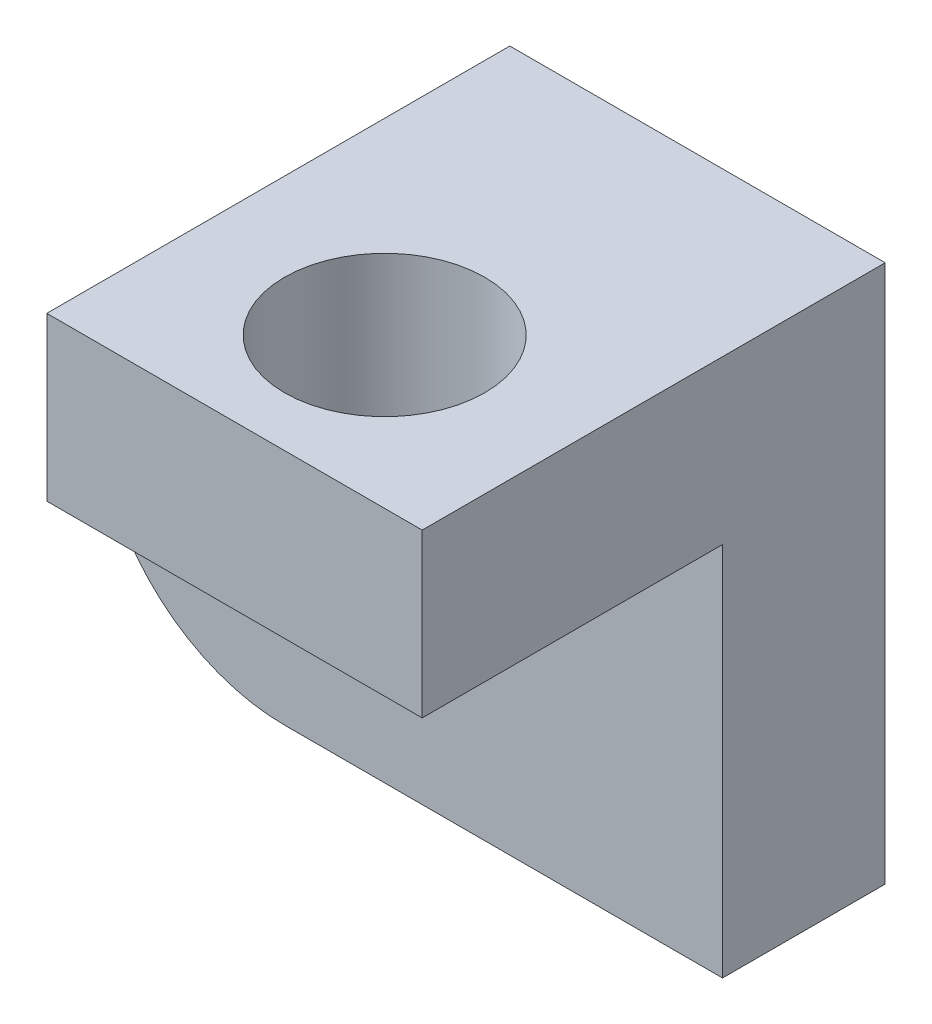
SolidWorks part; units mm, degrees
ref_plane "Front Plane" through (0, 0, 0) normal (0, 0, 1) x (1, 0, 0)
ref_plane "Top Plane" through (0, 0, 0) normal (0, 1, 0) x (1, 0, 0)
ref_plane "Right Plane" through (0, 0, 0) normal (1, 0, 0) x (0, 0, -1)
sketch "Sketch1" plane through (0, 0, 0) normal (0, 0, 1) x (1, 0, 0)
  line L0 (124, 287) -> (620, 287) construction
  line L1 (55, 0) -> (-55, 0) construction
  line L2 (-54.3261, 0) -> (-19.3261, 0)
  line L4 (-54.3261, 30) -> (-19.3261, 30)
  line L5 (-19.3261, 0) -> (-19.3261, 30)
  arc A0 (-54.3261, 30) -> (-54.3261, 0) centre (-54.3261, 15) ccw
  circle A1 centre (-54.3261, 15) radius 6.5
  dimension "D1" = 30
  dimension "D3" = 13
  dimension "D2" = 35
extrude "Boss-Extrude1" add sketch "Sketch1" along normal blind 13
sketch "Sketch3" plane through (0, 30, 0) normal (0, 1, 0) x (1, 0, 0)
  line L11 (-16.5, 0) -> (16.5, 0) construction
  line L12 (-19.3261, -13) -> (-49.3261, -13)
  line L13 (-19.3261, -13) -> (-19.3261, 0)
  line L14 (-19.3261, 0) -> (-49.3261, 0)
  line L15 (-49.3261, -13) -> (-49.3261, 0)
  dimension "D1" = 30
  dimension "D2" = 13
extrude "Boss-Extrude2" add sketch "Sketch3" along normal blind 13
sketch "Sketch6" plane through (0, 0, 13) normal (0, 0, 1) x (1, 0, 0)
  line L2 (-49.3261, 30) -> (-19.3261, 30)
  line L3 (-49.3261, 30) -> (-49.3261, 43)
  line L4 (-49.3261, 43) -> (-19.3261, 43)
  line L5 (-19.3261, 30) -> (-19.3261, 43)
extrude "Boss-Extrude4" add sketch "Sketch6" along normal blind 24
sketch "Sketch7" plane through (0, 30, 0) normal (0, -1, 0) x (1, 0, 0)
  line L0 (-19.3261, 25) -> (-49.3261, 25) construction
  line L5 (-34.3261, 37) -> (-34.3261, 13) construction
  circle A0 centre (-34.3261, 25) radius 8
  dimension "D1" = 16
extrude "Cut-Extrude1" cut sketch "Sketch7" against normal blind 13
